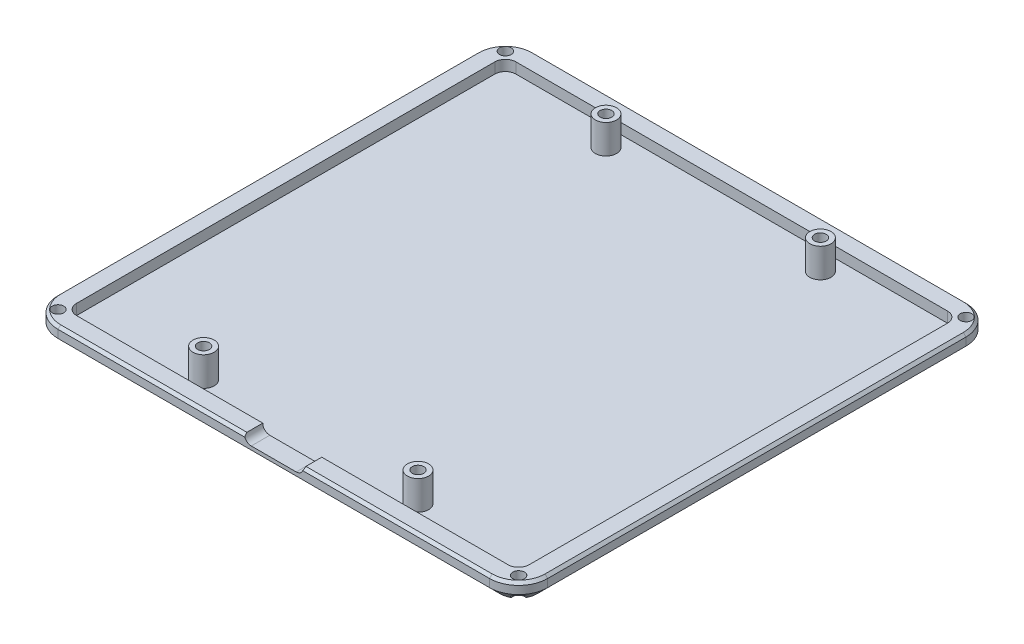
SolidWorks part; units mm, degrees
ref_plane "Front Plane" through (0, 0, 0) normal (0, 0, 1) x (1, 0, 0)
ref_plane "Top Plane" through (0, 0, 0) normal (0, 1, 0) x (1, 0, 0)
ref_plane "Right Plane" through (0, 0, 0) normal (1, 0, 0) x (0, 0, -1)
sketch "Sketch1" plane through (0, 0, 0) normal (0, 1, 0) x (1, 0, 0)
  line L0 (-42.7507, 39.5) -> (-42.7507, -39.5)
  line L5 (-40.75, -41.5007) -> (40.75, -41.5007)
  line L6 (42.7507, -39.5) -> (42.7507, 39.5)
  line L7 (40.75, 41.5007) -> (-40.75, 41.5007)
  line L8 (-42.7507, 0) -> (42.7507, 0) construction
  line L9 (0, 41.5007) -> (0, -41.5007) construction
  line L10 (40.75, 45.0007) -> (-40.75, 45.0007)
  line L11 (-46.2507, 39.5) -> (-46.2507, -39.5)
  line L12 (46.2507, -39.5) -> (46.2507, 39.5)
  line L13 (-40.75, -45.0007) -> (40.75, -45.0007)
  arc A0 (-40.75, 41.5007) -> (-42.7507, 39.5) centre (-40.75, 39.5) ccw
  arc A1 (-42.7507, -39.5) -> (-40.75, -41.5007) centre (-40.75, -39.5) ccw
  arc A2 (40.75, -41.5007) -> (42.7507, -39.5) centre (40.75, -39.5) ccw
  arc A3 (42.7507, 39.5) -> (40.75, 41.5007) centre (40.75, 39.5) ccw
  arc A4 (-46.2507, 39.5) -> (-40.75, 45.0007) centre (-40.75, 39.5) cw
  arc A5 (40.75, 45.0007) -> (46.2507, 39.5) centre (40.75, 39.5) cw
  arc A6 (40.75, -45.0007) -> (46.2507, -39.5) centre (40.75, -39.5) ccw
  arc A7 (-40.75, -45.0007) -> (-46.2507, -39.5) centre (-40.75, -39.5) cw
  point P16 (0, 0)
  point P22 (0, 0)
  dimension "D1" = 79
  dimension "D2" = 81.5
  dimension "D3" = 3.5
  dimension "D4" = 2.0007
extrude "Boss-Extrude1" add sketch "Sketch1" along normal blind 4 contours A7 L11 A4 L10 A5 L12 A6 L13
sketch "Sketch2" plane through (0, 4, 0) normal (0, 1, 0) x (1, 0, 0)
  line L1 (-42.7507, -41.5007) -> (42.7507, -41.5007) construction
  line L2 (-42.7507, -41.5007) -> (-42.7507, 41.5007) construction
  line L3 (-42.7507, 41.5007) -> (42.7507, 41.5007) construction
  line L4 (42.7507, -41.5007) -> (42.7507, 41.5007) construction
  line L5 (-42.7507, -41.5007) -> (42.7507, 41.5007) construction
  line L6 (-42.7507, 41.5007) -> (42.7507, -41.5007) construction
  line L7 (40.75, 41.5007) -> (-40.75, 41.5007) construction
  line L8 (42.7507, -39.5) -> (42.7507, 39.5) construction
  line L9 (-40.75, -41.5007) -> (40.75, -41.5007) construction
  line L10 (-42.7507, 39.5) -> (-42.7507, -39.5) construction
  line L11 (-42.7507, 39.5) -> (-42.7507, -39.5)
  line L12 (-40.75, -41.5007) -> (40.75, -41.5007)
  line L13 (42.7507, -39.5) -> (42.7507, 39.5)
  line L14 (40.75, 41.5007) -> (-40.75, 41.5007)
  arc A0 (-42.7507, 39.5) -> (-40.75, 41.5007) centre (-40.75, 39.5) cw
  arc A1 (40.75, 41.5007) -> (42.7507, 39.5) centre (40.75, 39.5) cw
  arc A2 (40.75, -41.5007) -> (42.7507, -39.5) centre (40.75, -39.5) ccw
  arc A3 (-40.75, -41.5007) -> (-42.7507, -39.5) centre (-40.75, -39.5) cw
extrude "Cut-Extrude1" cut sketch "Sketch2" against normal blind 2 contours L14 A0 L11 A3 L12 A2 L13 A1
sketch "Sketch3" plane through (0, 0, 45.0007) normal (0, 0, 1) x (1, 0, 0)
  line L0 (-4.25, 4) -> (4.25, 4) construction
  line L1 (-40.75, 4) -> (40.75, 4) construction
  line L2 (-4.25, 5.325) -> (4.25, 5.325)
  line L3 (-4.25, 2.675) -> (4.25, 2.675)
  arc A0 (-4.25, 5.325) -> (-4.25, 2.675) centre (-4.25, 4) ccw
  arc A1 (4.25, 2.675) -> (4.25, 5.325) centre (4.25, 4) ccw
  point P4 (0, 4)
  dimension "D1" = 2.65
  dimension "D2" = 8.5
extrude "Cut-Extrude2" cut sketch "Sketch3" against normal up to surface (3.5 mm away) up to face at (0, 3, 41.5007)
chamfer "Chamfer2" distance 2 angle 45 8 edges at (46.2507, 0, 0) (44.6396, 0, -43.3896) (44.6396, 0, 43.3896) (0, 0, -45.0007) (0, 0, 45.0007) (-44.6396, 0, -43.3896) (-44.6396, 0, 43.3896) (-46.2507, 0, 0)
chamfer "Chamfer3" distance 0.5 angle 45 9 edges at (-23.1625, 4, 45.0007) (-44.6396, 4, 43.3896) (-46.2507, 4, 0) (-44.6396, 4, -43.3896) (0, 4, -45.0007) (44.6396, 4, -43.3896) (46.2507, 4, 0) (44.6396, 4, 43.3896) (23.1625, 4, 45.0007)
sketch "Sketch4" plane through (0, 2, 0) normal (0, 1, 0) x (1, 0, 0)
  line L0 (-42.7507, 39.5) -> (-42.7507, -39.5) construction
  line L1 (-40.75, -41.5007) -> (-5.575, -41.5007) construction
  line L2 (0, 45.0007) -> (0, -45.0007) construction
  line L3 (-40.75, 45.0007) -> (40.75, 45.0007) construction
  line L4 (-4.25, -45.0007) -> (4.25, -45.0007) construction
  line L5 (-42.7507, 0) -> (42.7507, 0) construction
  line L6 (-42.7507, 39.5) -> (-42.7507, -39.5) construction
  line L7 (42.7507, -39.5) -> (42.7507, 39.5) construction
  circle A0 centre (-20.2507, -38.0007) radius 2
  circle A1 centre (20.2507, -38.0007) radius 2
  circle A2 centre (20.2507, 38.0007) radius 2
  circle A3 centre (-20.2507, 38.0007) radius 2
  circle A4 centre (-20.2507, -38.0007) radius 1.1
  circle A5 centre (20.2507, -38.0007) radius 1.1
  circle A6 centre (20.2507, 38.0007) radius 1.1
  circle A7 centre (-20.2507, 38.0007) radius 1.1
  dimension "D3" = 4
  dimension "D4" = 2.2
  dimension "D1" = 22.5
  dimension "D2" = 3.5
extrude "Boss-Extrude2" add sketch "Sketch4" along normal blind 5.5
sketch "Sketch5" plane through (0, 0, 0) normal (0, -1, 0) x (1, 0, 0)
  line L0 (-46.2507, 39.5) -> (-40.75, 45.0007) construction
  line L1 (-46.2507, 0) -> (46.2507, 0) construction
  line L2 (-46.2507, -39.5) -> (-46.2507, 39.5) construction
  line L3 (46.2507, 39.5) -> (46.2507, -39.5) construction
  line L4 (0, 45.0007) -> (0, -45.0007) construction
  line L5 (-40.75, 45.0007) -> (40.75, 45.0007) construction
  line L6 (40.75, -45.0007) -> (-40.75, -45.0007) construction
  circle A0 centre (-43.5004, 42.2504) radius 1.1
  circle A1 centre (43.5004, 42.2504) radius 1.1
  circle A2 centre (43.5004, -42.2504) radius 1.1
  circle A3 centre (-43.5004, -42.2504) radius 1.1
  point P20 (0, 0)
  dimension "D1" = 2.2
extrude "Cut-Extrude3" cut sketch "Sketch5" against normal up to surface (4 mm away) up to face at (0, 4, 8.6001)
